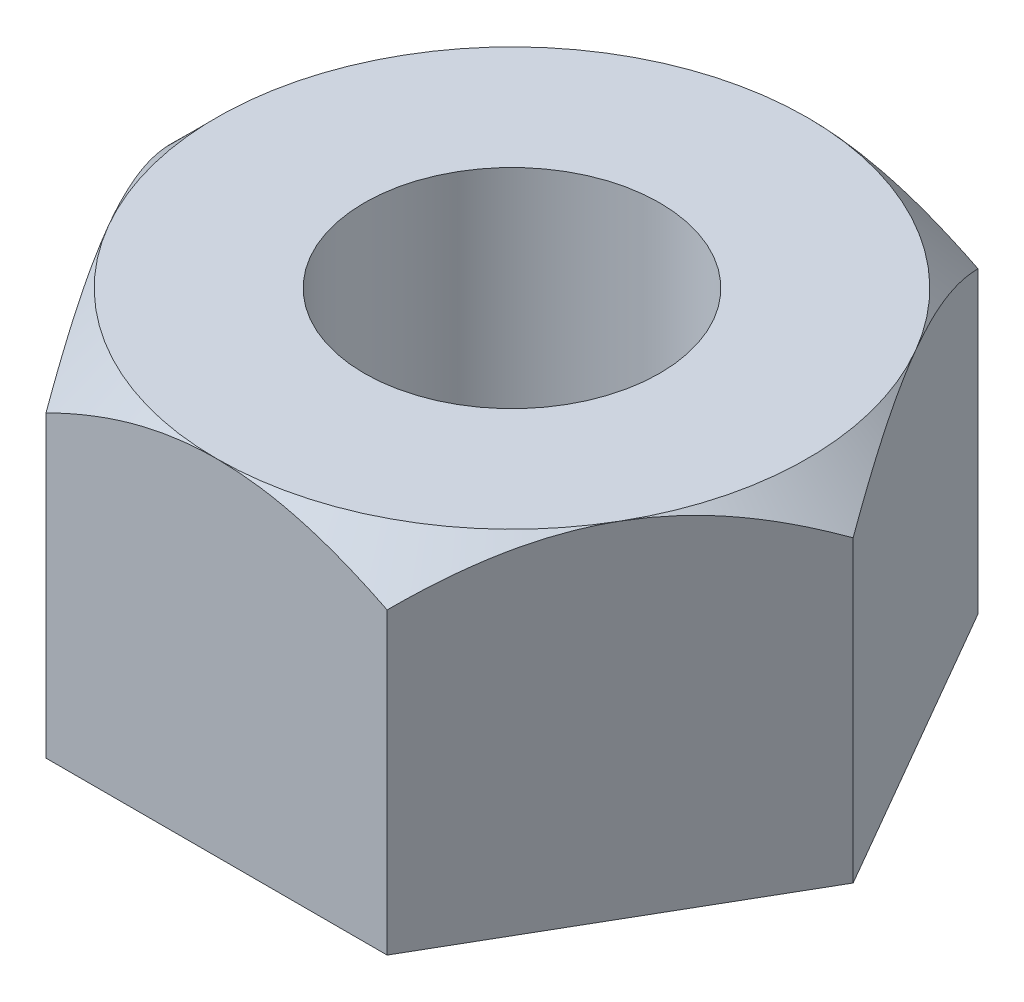
SolidWorks part; units mm, degrees
ref_plane "Front Plane" through (0, 0, 0) normal (0, 0, 1) x (1, 0, 0)
ref_plane "Top Plane" through (0, 0, 0) normal (0, 1, 0) x (1, 0, 0)
ref_plane "Right Plane" through (0, 0, 0) normal (1, 0, 0) x (0, 0, -1)
sketch "Sketch1" plane through (0, 0, 0) normal (0, 1, 0) x (1, 0, 0)
  line L1 (34.641, 0) -> (17.3205, 30)
  line L2 (17.3205, 30) -> (-17.3205, 30)
  line L3 (-17.3205, 30) -> (-34.641, 0)
  line L4 (-34.641, 0) -> (-17.3205, -30)
  line L5 (-17.3205, -30) -> (17.3205, -30)
  line L6 (17.3205, -30) -> (34.641, 0)
  circle A0 centre (0, 0) radius 30 construction
  circle A1 centre (0, 0) radius 15
  dimension "D2" = 30
  dimension "D1" = 60
extrude "Boss-Extrude1" add sketch "Sketch1" along normal blind 35
sketch "Sketch2" plane through (0, 35, 0) normal (0, 1, 0) x (1, 0, 0)
  circle A0 centre (0, 0) radius 30
  dimension "D1" = 60
extrude "Cut-Extrude1" cut sketch "Sketch2" against normal blind 10 draft 45 flip side to cut
